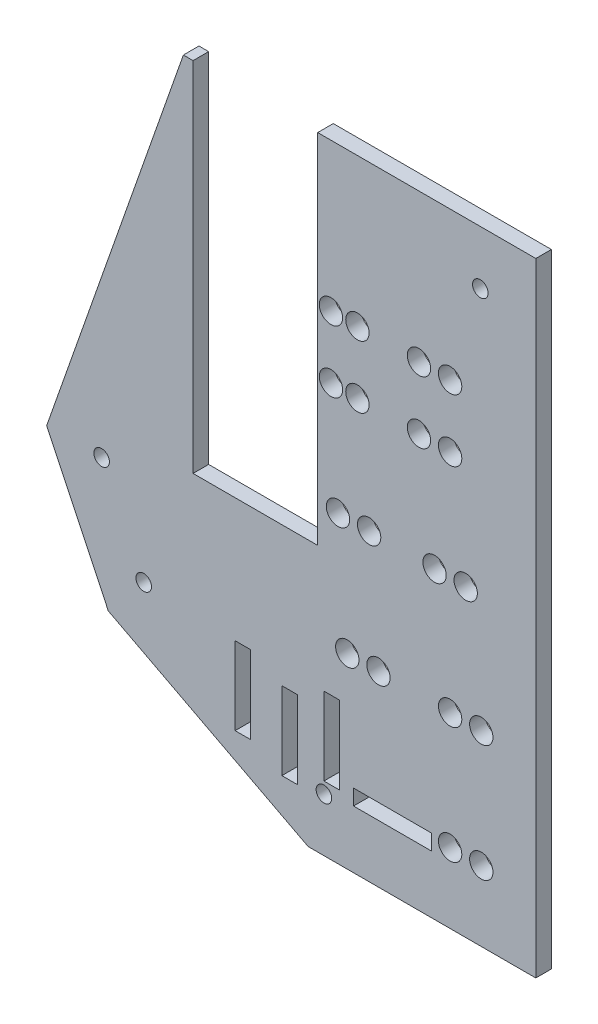
SolidWorks part; units mm, degrees
ref_plane "Front Plane" through (0, 0, 0) normal (0, 0, 1) x (1, 0, 0)
ref_plane "Top Plane" through (0, 0, 0) normal (0, 1, 0) x (1, 0, 0)
ref_plane "Right Plane" through (0, 0, 0) normal (1, 0, 0) x (0, 0, -1)
sketch "Sketch1" plane through (0, 0, 0) normal (0, 0, 1) x (1, 0, 0)
  line L6 (-20.066, -57.15) -> (46.99, -57.15) construction
  line L7 (-12.446, -73.152) -> (46.99, -73.152) construction
  line L8 (-4.1204, 6.35) -> (53.34, 6.35)
  line L9 (53.34, 6.35) -> (53.34, -95.25)
  line L10 (53.34, -95.25) -> (16.225, -95.25)
  line L16 (-4.1204, 6.35) -> (-26.416, -57.15)
  line L18 (-20.066, -57.15) -> (-26.416, -57.15) construction
  line L26 (0, 0) -> (46.99, 0) construction
  line L27 (46.99, 0) -> (46.99, -88.9) construction
  line L28 (46.99, -88.9) -> (17.78, -88.9) construction
  line L29 (17.78, -88.9) -> (-12.446, -73.152) construction
  line L30 (-12.446, -73.152) -> (-20.066, -57.15) construction
  line L31 (-20.066, -57.15) -> (0, 0) construction
  line L32 (46.99, -57.15) -> (46.99, -88.9) construction
  line L33 (17.78, -88.9) -> (16.225, -95.25) construction
  line L34 (-12.446, -73.152) -> (-17.9301, -78.4424) construction
  line L35 (16.225, -95.25) -> (-16.3566, -78.2747)
  line L36 (-26.416, -57.15) -> (-16.3566, -78.2747)
  point P40 (24.6098, 6.35)
  dimension "D1" = 88.9
  dimension "D2" = 29.21
  dimension "D3" = 59.436
  dimension "D4" = 67.056
  dimension "D5" = 6.35
  dimension "D6" = 6.35
  dimension "D7" = 46.99
  dimension "D8" = 6.35
  dimension "D13" = 103.76
  dimension "D14" = 6.35
  dimension "D17" = 108.51
  dimension "D22" = 5.7332
extrude "Boss-Extrude1" add sketch "Sketch1" along normal blind 2.54
sketch "Sketch3" plane through (0, 0, 0) normal (0, 0, 1) x (1, 0, 0)
  line L8 (0, 0) -> (46.99, 0) construction
  line L9 (46.99, 0) -> (46.99, -88.9) construction
  line L10 (46.99, -88.9) -> (17.78, -88.9) construction
  line L11 (17.78, -88.9) -> (-12.446, -73.152) construction
  line L12 (-12.446, -73.152) -> (-20.066, -57.15) construction
  line L13 (-20.066, -57.15) -> (0, 0) construction
sketch "Sketch4" plane through (0, 0, 0) normal (0, 0, -1) x (-1, 0, 0)
  line L8 (-17.78, -1.143) -> (2.54, -1.143)
  line L9 (-17.78, -1.143) -> (-17.78, -51.943)
  line L10 (-17.78, -51.943) -> (2.54, -51.943)
  line L11 (2.54, -1.143) -> (2.54, -51.943)
  circle A0 centre (-39.37, -17.78) radius 1.905
  circle A1 centre (-34.29, -17.78) radius 1.905
  circle A2 centre (-39.37, -27.94) radius 1.905
  circle A3 centre (-34.29, -27.94) radius 1.905
  circle A4 centre (-41.91, -45.72) radius 1.905
  circle A5 centre (-36.83, -45.72) radius 1.905
  circle A6 centre (-44.45, -64.77) radius 1.905
  circle A7 centre (-39.37, -64.77) radius 1.905
  circle A8 centre (-44.45, -83.82) radius 1.905
  circle A9 centre (-39.37, -83.82) radius 1.905
  circle A10 centre (-24.257, -17.78) radius 1.905
  circle A11 centre (-19.939, -17.78) radius 1.905
  circle A12 centre (-24.257, -27.94) radius 1.905
  circle A13 centre (-19.939, -27.94) radius 1.905
  circle A14 centre (-26.162, -45.72) radius 1.905
  circle A15 centre (-21.082, -45.72) radius 1.905
  circle A16 centre (-27.686, -64.77) radius 1.905
  circle A17 centre (-22.606, -64.77) radius 1.905
  dimension "D1" = 3.81
  dimension "D2" = 3.81
  dimension "D6" = 3.81
  dimension "D7" = 3.81
  dimension "D11" = 3.81
  dimension "D12" = 3.81
  dimension "D16" = 3.81
  dimension "D17" = 3.81
  dimension "D21" = 3.81
  dimension "D22" = 3.81
  dimension "D30" = 3.81
  dimension "D31" = 3.81
  dimension "D35" = 3.81
  dimension "D36" = 3.81
  dimension "D40" = 3.81
  dimension "D41" = 3.81
  dimension "D45" = 3.81
  dimension "D46" = 3.81
  dimension "D3" = 5.08
  dimension "D8" = 5.08
  dimension "D13" = 5.08
  dimension "D18" = 5.08
  dimension "D23" = 5.08
  dimension "D26" = 50.8
  dimension "D27" = 20.32
  dimension "D32" = 4.318
  dimension "D37" = 4.318
  dimension "D42" = 5.08
  dimension "D47" = 5.08
extrude "Cut-Extrude2" cut sketch "Sketch4" against normal blind 25.4
sketch "Sketch5" plane through (0, 0, 2.54) normal (0, 0, 1) x (1, 0, 0)
  line L0 (-2.54, -1.143) -> (-2.54, 6.35)
  line L1 (53.34, 6.35) -> (-4.1204, 6.35) construction
  line L2 (17.78, -1.143) -> (17.78, 6.35)
  line L3 (17.78, 6.35) -> (-2.54, 6.35)
  line L4 (-2.54, -1.143) -> (17.78, -1.143)
extrude "Cut-Extrude3" cut sketch "Sketch5" against normal blind 5.08
sketch "Sketch6" plane through (0, 0, 2.54) normal (0, 0, 1) x (1, 0, 0)
  line L0 (0, 0) -> (46.99, 0) construction
  line L1 (46.99, 0) -> (46.99, -88.9) construction
  line L2 (17.78, -88.9) -> (17.78, -82.3142) construction
  line L3 (46.99, -88.9) -> (17.78, -88.9) construction
  circle A0 centre (1.6002, -2.4384) radius 1.27
  circle A1 centre (44.2976, -2.4384) radius 1.27
  circle A2 centre (-17.4498, -57.15) radius 1.27
  circle A4 centre (-10.5918, -71.3486) radius 1.27
  circle A5 centre (18.796, -86.5378) radius 1.27
  dimension "D1" = 2.54
  dimension "D3" = 2.54
  dimension "D7" = 2.54
  dimension "D9" = 2.54
  dimension "D11" = 2.54
  dimension "D2" = 2.4384
  dimension "D4" = 2.4384
  dimension "D5" = 2.6924
  dimension "D6" = 45.3898
  dimension "D8" = 2.6162
  dimension "D10" = 2.5866
  dimension "D12" = 1.016
  dimension "D13" = 2.3622
extrude "Cut-Extrude4" cut sketch "Sketch6" against normal blind 5.08
sketch "Sketch8" plane through (0, 0, 2.54) normal (0, 0, 1) x (1, 0, 0)
  line L0 (46.99, 0) -> (46.99, -88.9) construction
  line L1 (23.622, -83.2866) -> (36.322, -83.2866)
  line L2 (23.622, -83.2866) -> (23.622, -85.8266)
  line L3 (23.622, -85.8266) -> (36.322, -85.8266)
  line L4 (36.322, -83.2866) -> (36.322, -85.8266)
  line L5 (0, 0) -> (46.99, 0) construction
  line L7 (18.796, -72.009) -> (21.336, -72.009)
  line L8 (18.796, -72.009) -> (18.796, -84.709)
  line L9 (18.796, -84.709) -> (21.336, -84.709)
  line L10 (21.336, -72.009) -> (21.336, -84.709)
  line L11 (11.938, -74.676) -> (14.478, -74.676)
  line L12 (11.938, -74.676) -> (11.938, -87.376)
  line L13 (11.938, -87.376) -> (14.478, -87.376)
  line L14 (14.478, -74.676) -> (14.478, -87.376)
  line L15 (4.318, -72.136) -> (6.858, -72.136)
  line L16 (4.318, -72.136) -> (4.318, -84.836)
  line L17 (4.318, -84.836) -> (6.858, -84.836)
  line L18 (6.858, -72.136) -> (6.858, -84.836)
  dimension "D1" = 12.7
  dimension "D2" = 2.54
  dimension "D3" = 10.668
  dimension "D4" = 83.2866
  dimension "D5" = 12.7
  dimension "D6" = 2.54
  dimension "D7" = 25.654
  dimension "D8" = 72.009
  dimension "D9" = 12.7
  dimension "D10" = 2.54
  dimension "D11" = 32.512
  dimension "D12" = 74.676
  dimension "D13" = 12.7
  dimension "D14" = 2.54
  dimension "D15" = 72.136
  dimension "D16" = 40.132
extrude "Cut-Extrude5" cut sketch "Sketch8" against normal blind 5.08
